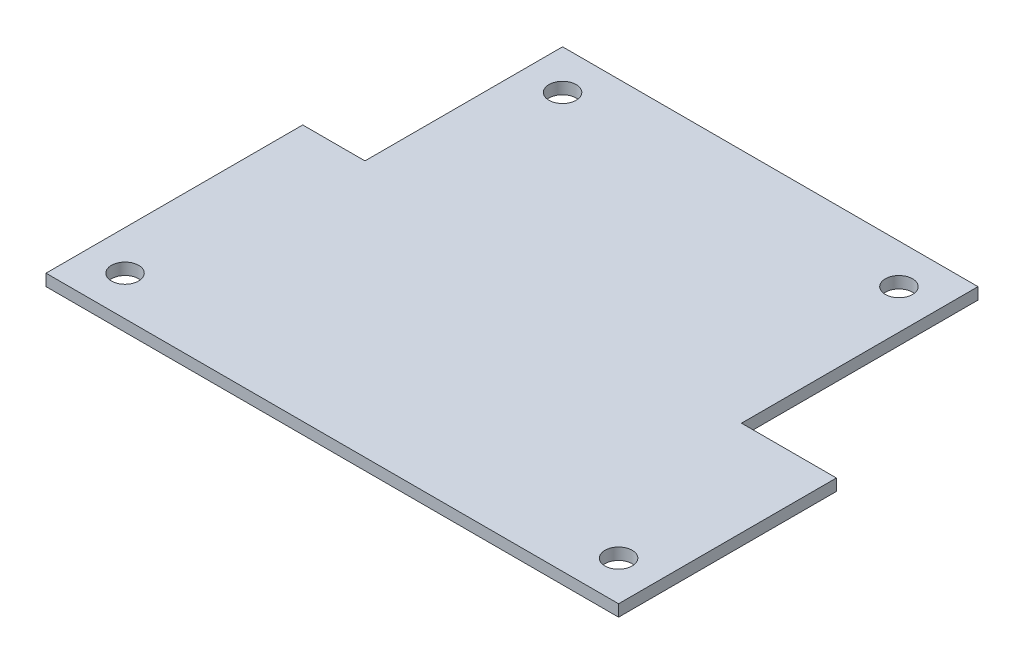
SolidWorks part; units mm, degrees
ref_plane "Front Plane" through (0, 0, 0) normal (0, 0, 1) x (1, 0, 0)
ref_plane "Top Plane" through (0, 0, 0) normal (0, 1, 0) x (1, 0, 0)
ref_plane "Right Plane" through (0, 0, 0) normal (1, 0, 0) x (0, 0, -1)
sketch "Sketch1" plane through (0, 0, 0) normal (0, 1, 0) x (1, 0, 0)
  line L0 (0, 0) -> (73.6, 0)
  line L1 (73.6, 0) -> (73.6, 28)
  line L2 (73.6, 28) -> (61.4, 28)
  line L3 (61.4, 28) -> (61.4, 58.4)
  line L4 (61.4, 58.4) -> (8, 58.4)
  line L5 (8, 58.4) -> (8, 33)
  line L6 (8, 33) -> (0, 33)
  line L7 (0, 33) -> (0, 0)
  circle A0 centre (5.08, 5.08) radius 1.75
  circle A1 centre (68.52, 5.08) radius 1.75
  circle A2 centre (13.08, 53.32) radius 1.75
  circle A3 centre (56.32, 53.32) radius 1.75
  dimension "D8" = 3.5
  dimension "D9" = 3.5
  dimension "D10" = 3.5
  dimension "D11" = 3.5
  dimension "D1" = 73.6
  dimension "D2" = 58.4
  dimension "D3" = 28
  dimension "D4" = 33
  dimension "D5" = 53.4
  dimension "D6" = 8
  dimension "D7" = 12.2
  dimension "D12" = 5.08
  dimension "D13" = 5.08
  dimension "D14" = 5.08
  dimension "D15" = 5.08
  dimension "D16" = 5.08
  dimension "D17" = 5.08
  dimension "D18" = 5.08
  dimension "D19" = 5.08
extrude "Boss-Extrude1" add sketch "Sketch1" along normal blind 1.5
